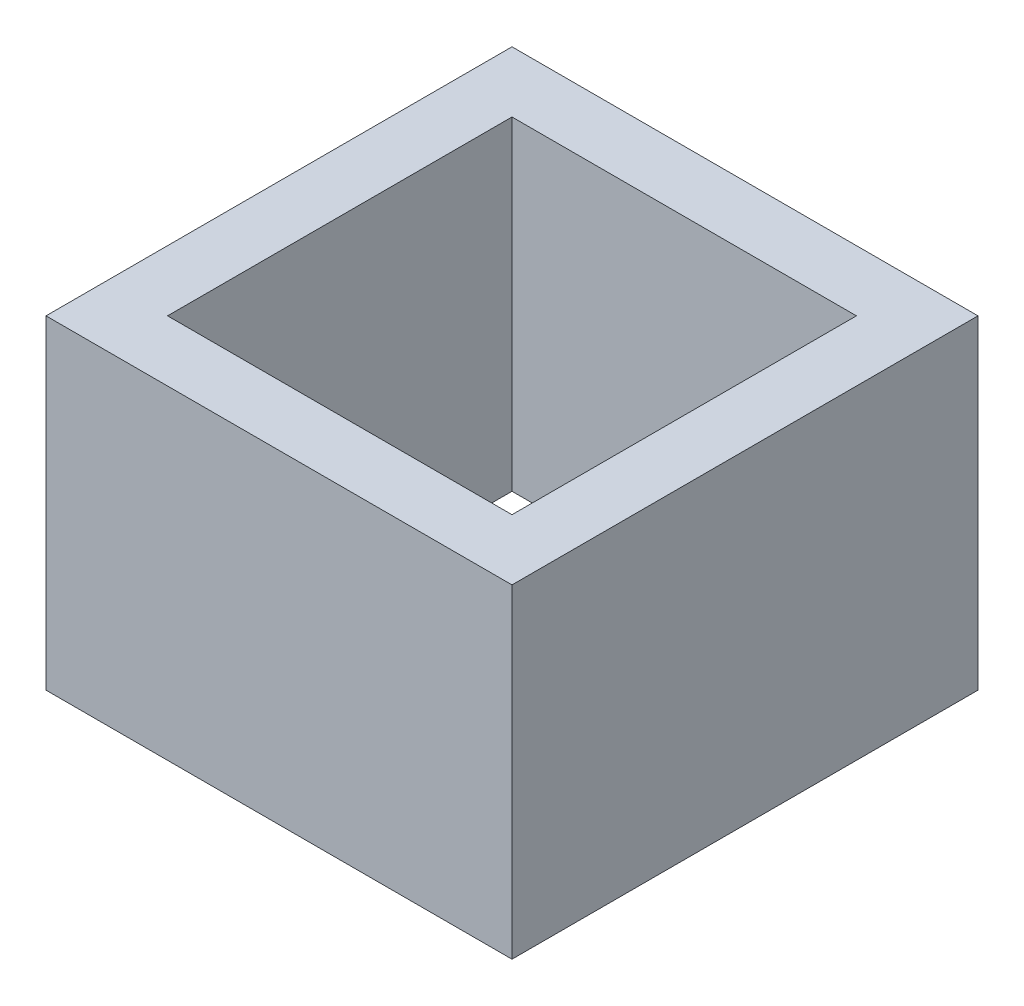
SolidWorks part; units mm, degrees
ref_plane "Front Plane" through (0, 0, 0) normal (0, 0, 1) x (1, 0, 0)
ref_plane "Top Plane" through (0, 0, 0) normal (0, 1, 0) x (1, 0, 0)
ref_plane "Right Plane" through (0, 0, 0) normal (1, 0, 0) x (0, 0, -1)
sketch "Sketch1" plane through (0, 0, 0) normal (0, 1, 0) x (1, 0, 0)
  line L1 (4.25, -4.25) -> (-4.25, -4.25)
  line L2 (4.25, -4.25) -> (4.25, 4.25)
  line L3 (4.25, 4.25) -> (-4.25, 4.25)
  line L4 (-4.25, -4.25) -> (-4.25, 4.25)
  line L5 (4.25, -4.25) -> (-4.25, 4.25) construction
  line L6 (4.25, 4.25) -> (-4.25, -4.25) construction
  line L7 (5.75, -5.75) -> (-5.75, -5.75)
  line L8 (5.75, -5.75) -> (5.75, 5.75)
  line L9 (5.75, 5.75) -> (-5.75, 5.75)
  line L10 (-5.75, -5.75) -> (-5.75, 5.75)
  line L11 (5.75, -5.75) -> (-5.75, 5.75) construction
  line L12 (5.75, 5.75) -> (-5.75, -5.75) construction
  point P0 (0, 0)
  point P6 (0, 0)
  dimension "D1" = 1.5
  dimension "D2" = 1.5
  dimension "D3" = 8.5
  dimension "D4" = 8.5
extrude "Boss-Extrude1" add sketch "Sketch1" along normal blind 8
